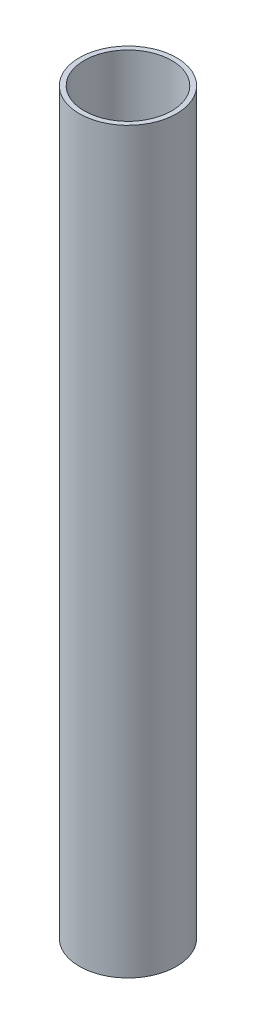
SolidWorks part; units mm, degrees
material "1060 Alloy"
ref_plane "Front Plane" through (0, 0, 0) normal (0, 0, 1) x (1, 0, 0)
ref_plane "Top Plane" through (0, 0, 0) normal (0, 1, 0) x (1, 0, 0)
ref_plane "Right Plane" through (0, 0, 0) normal (1, 0, 0) x (0, 0, -1)
sketch "Sketch1" plane through (0, 0, 0) normal (0, 1, 0) x (1, 0, 0)
  circle A0 centre (-15.4613, 4.5021) radius 20
  circle A1 centre (-15.4613, 4.5021) radius 18
  dimension "D1" = 36
  dimension "D2" = 40
extrude "Boss-Extrude1" add sketch "Sketch1" along normal blind 304
